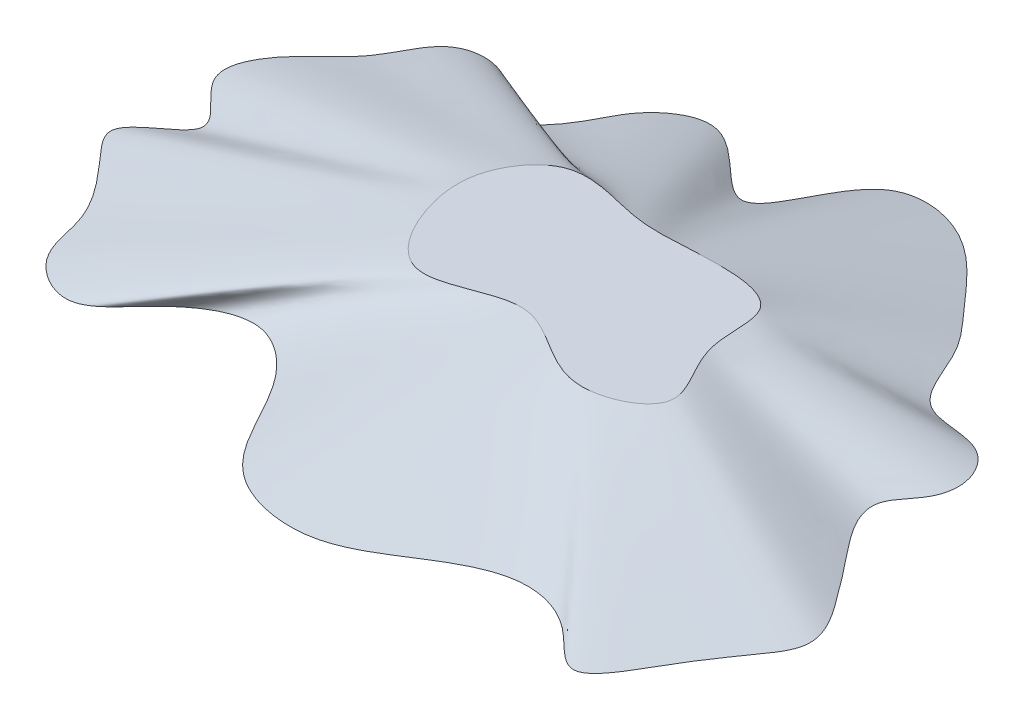
SolidWorks part; units mm, degrees
ref_plane "Front Plane" through (0, 0, 0) normal (0, 0, 1) x (1, 0, 0)
ref_plane "Top Plane" through (0, 0, 0) normal (0, 1, 0) x (1, 0, 0)
ref_plane "Right Plane" through (0, 0, 0) normal (1, 0, 0) x (0, 0, -1)
sketch "Sketch2" plane through (0, 0, 0) normal (0, 1, 0) x (1, 0, 0)
  circle A0 centre (0, 0) radius 63.5 construction
  spline S0 degree 3 poles (-88.1114, -25.3513) (-99.2891, -12.5842) (-76.679, -4.0824) (-97.6885, 6.542) (-90.634, 22.0518) (-79.0024, 29.1718) (-74.0783, 44.6344) (-58.3453, 45.2314) (-50.6259, 30.2543) (-40.7332, 42.1778) (-37.2023, 51.9408) (-21.2896, 63.4514) (-3.0726, 33.0261) (3.9646, 68.5497) (29.0701, 66.7129) (40.3187, 52.2197) (52.6041, 39.3746) (56.5276, 21.8915) (73.5812, 24.9196) (79.8572, 14.7231) (78.3049, 6.2185) (69.1856, -1.8508) (79.9617, -15.2216) (87.891, -25.3216) (95.9252, -37.1233) (89.2014, -46.8808) (83.3757, -54.9365) (78.8519, -63.3871) (70.9519, -75.2011) (60.6026, -61.326) (44.6671, -57.3981) (28.8247, -67.1436) (12.7203, -77.7519) (-15.4584, -72.3026) (-19.9604, -47.4882) (-39.4292, -34.8011) (-53.6062, -44.3097) (-63.9322, -58.8519) (-78.5773, -49.9622) (-79.9806, -34.456) (-88.1114, -25.3513) (-99.2891, -12.5842) (-76.679, -4.0824) knots -0.065555 -0.046557 -0.011923 0 0.025837 0.052027 0.070243 0.099398 0.123093 0.142833 0.165491 0.183417 0.201302 0.224727 0.262346 0.304235 0.329158 0.373004 0.393177 0.422471 0.447241 0.463072 0.475278 0.489382 0.517812 0.541072 0.564343 0.578736 0.596948 0.61542 0.632111 0.652467 0.681115 0.712226 0.742742 0.779098 0.836615 0.854872 0.887306 0.91177 0.934445 0.953443 0.988077 1 1.025837 1.052027 1.070243 only from (-95.2285, -15.2014) to (-95.2285, -15.2014)
  dimension "D1" = 127
ref_plane "Plane1" through (0, 12.7, 0) normal (0, 1, 0) x (1, 0, 0)
sketch "Sketch3" plane through (0, 12.7, 0) normal (0, 1, 0) x (1, 0, 0)
  spline S0 degree 3 poles (-19.0902, -26.9384) (-30.5455, -5.7424) (-30.7126, 8.9867) (-20.2385, 22.6843) (-2.4716, 15.1698) (13.293, 17.2081) (35.1676, 16.5945) (30.8298, -3.1166) (45.5831, -17.9785) (20.7413, -29.8796) (5.5093, -8.159) (-19.0902, -26.9384) (-30.5455, -5.7424) (-30.7126, 8.9867) knots -0.347829 -0.216054 -0.106147 0 0.065471 0.130018 0.229536 0.315426 0.407699 0.48553 0.573499 0.652171 0.783946 0.893853 1 1.065471 1.130018 1.229536 only from (-29.5757, -3.5283) to (-29.5757, -3.5283)
loft "Loft2" add profiles "Sketch2", "Sketch3"
